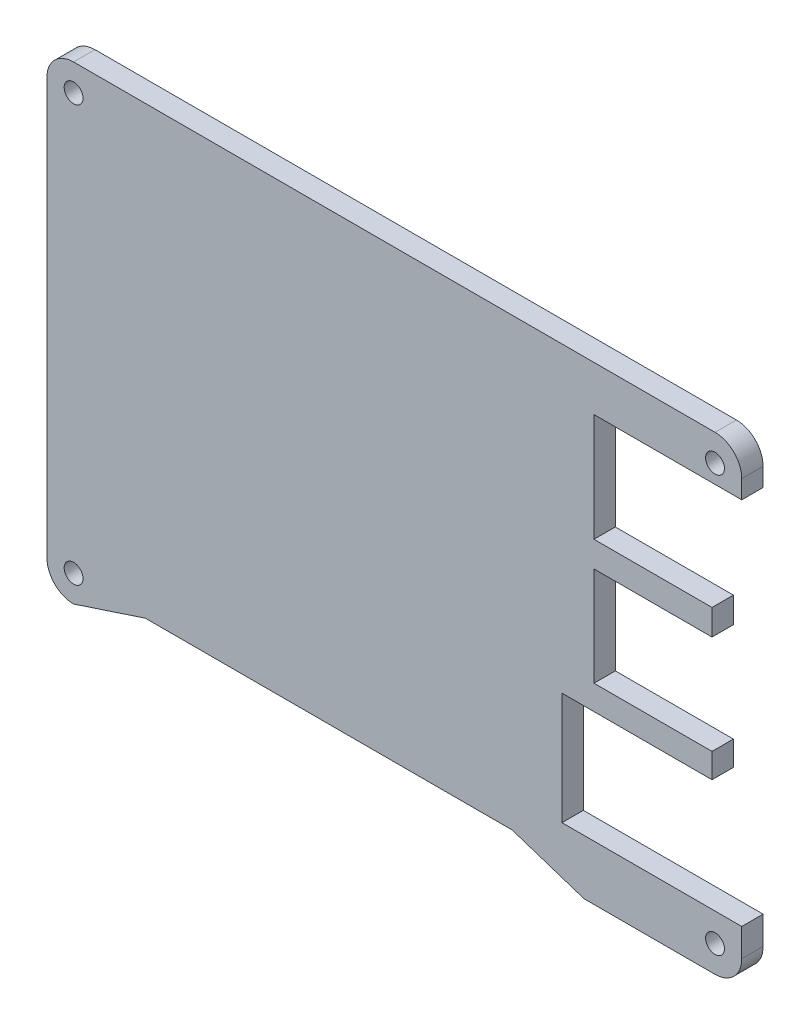
SolidWorks part; units mm, degrees
ref_plane "Front Plane" through (0, 0, 0) normal (0, 0, 1) x (1, 0, 0)
ref_plane "Top Plane" through (0, 0, 0) normal (0, 1, 0) x (1, 0, 0)
ref_plane "Right Plane" through (0, 0, 0) normal (1, 0, 0) x (0, 0, -1)
sketch "Sketch1" plane through (0, 0, 0) normal (0, 0, 1) x (1, 0, 0)
  line L1 (61.2149, 24.0683) -> (61.2149, 26.6839) construction
  line L2 (57.4049, 30.5077) -> (-34.0849, 30.5077) construction
  line L5 (56.975, 4.9979) -> (56.975, 8.6582) construction
  line L9 (56.975, -12.628) -> (56.975, -9.1218) construction
  line L10 (35.575, -12.628) -> (56.975, -12.628) construction
  line L11 (35.575, -28.6278) -> (35.575, -12.628) construction
  line L12 (61.2149, -28.6278) -> (35.575, -28.6278) construction
  line L13 (61.2149, -32.6134) -> (61.2149, -28.6278) construction
  line L14 (38.7143, -36.451) -> (57.405, -36.451) construction
  line L15 (28.4743, -33.0844) -> (38.7143, -36.451) construction
  line L16 (-23.8449, -33.0844) -> (28.4743, -33.0844) construction
  line L17 (-34.0849, -36.451) -> (-23.8449, -33.0844) construction
  line L18 (-37.8949, 26.6977) -> (-37.8949, -32.641) construction
  line L19 (61.2149, 24.0683) -> (40.1348, 24.0683)
  line L20 (61.2149, 24.0683) -> (61.2149, 26.6839)
  line L21 (57.4049, 30.5077) -> (-34.0849, 30.5077)
  line L22 (40.1348, 24.0683) -> (40.1348, 8.6582)
  line L23 (40.1348, 8.6582) -> (56.975, 8.6582)
  line L24 (56.975, 4.9979) -> (56.975, 8.6582)
  line L25 (56.975, 4.9979) -> (40.1348, 4.9979)
  line L26 (40.1348, 4.9979) -> (40.1348, -9.1218)
  line L27 (40.1348, -9.1218) -> (56.975, -9.1218)
  line L28 (56.975, -12.628) -> (56.975, -9.1218)
  line L29 (35.575, -12.628) -> (56.975, -12.628)
  line L30 (35.575, -28.6278) -> (35.575, -12.628)
  line L31 (61.2149, -28.6278) -> (35.575, -28.6278)
  line L32 (61.2149, -32.6134) -> (61.2149, -28.6278)
  line L33 (38.7143, -36.451) -> (57.405, -36.451)
  line L34 (28.4743, -33.0844) -> (38.7143, -36.451)
  line L35 (-23.8449, -33.0844) -> (28.4743, -33.0844)
  line L36 (-34.0849, -36.451) -> (-23.8449, -33.0844)
  line L37 (-37.8949, 26.6977) -> (-37.8949, -32.641)
  line L38 (-23.4169, -23.6989) -> (-23.4169, 9.8012) construction
  line L39 (-29.0049, 25.897) -> (31.6883, 25.897)
  line L40 (-29.0049, 25.897) -> (-29.0049, 18.087)
  line L41 (-29.0049, 18.087) -> (31.6883, 18.087)
  line L42 (31.6883, 25.897) -> (31.6883, 18.087)
  line L43 (-29.0049, 9.8012) -> (-23.4169, 9.8012)
  line L44 (-29.0049, 9.8012) -> (-29.0049, -13.5668)
  line L45 (-29.0049, -13.5668) -> (-23.4169, -13.5668)
  line L46 (-23.4169, 9.8012) -> (-23.4169, -13.5668)
  line L47 (-29.0049, 9.2932) -> (-23.4169, 9.2932)
  line L50 (13.845, -8.3602) -> (19.2484, -8.3602)
  line L51 (13.845, -8.3602) -> (13.845, -30.9668)
  line L52 (13.845, -30.9668) -> (19.2484, -30.9668)
  line L53 (19.2484, -8.3602) -> (19.2484, -30.9668)
  arc A0 (61.2149, 26.6839) -> (57.4049, 30.5077) centre (57.4049, 26.6977) ccw construction
  circle A1 centre (57.4049, 26.6977) radius 1.3462 construction
  arc A2 (57.405, -36.451) -> (61.2149, -32.6134) centre (57.405, -32.641) ccw construction
  arc A3 (-37.8949, -32.641) -> (-34.0849, -36.451) centre (-34.0849, -32.641) ccw construction
  arc A4 (-34.0849, 30.5077) -> (-37.8949, 26.6977) centre (-34.0849, 26.6977) ccw construction
  circle A5 centre (-34.0849, 26.6977) radius 1.3462 construction
  circle A6 centre (-34.0849, -32.641) radius 1.3462 construction
  arc A7 (61.2149, 26.6839) -> (57.4049, 30.5077) centre (57.4049, 26.6977) ccw
  circle A8 centre (57.4049, 26.6977) radius 1.3462
  arc A9 (57.405, -36.451) -> (61.2149, -32.6134) centre (57.405, -32.641) ccw
  arc A10 (-37.8949, -32.641) -> (-34.0849, -36.451) centre (-34.0849, -32.641) ccw
  arc A11 (-34.0849, 30.5077) -> (-37.8949, 26.6977) centre (-34.0849, 26.6977) ccw
  circle A12 centre (-34.0849, 26.6977) radius 1.3462
  circle A13 centre (-34.0849, -32.641) radius 1.3462
  circle A14 centre (57.405, -32.641) radius 1.3462 construction
  circle A15 centre (57.405, -32.641) radius 1.3462
  dimension "D1" = 23.368
  dimension "D2" = 0.508
  dimension "D3" = 16.8402
  dimension "D4" = 16.8402
extrude "Boss-Extrude1" add sketch "Sketch1" along normal blind 3.048
sketch "Sketch2" plane through (0, 0, 3.048) normal (0, 0, 1) x (1, 0, 0)
  line L2 (-37.8949, 26.6977) -> (-37.8949, -32.641) construction
  line L5 (57.4049, 30.5077) -> (-34.0849, 30.5077) construction
  line L6 (-10.2851, -8.9639) -> (-10.2851, 8.0033) construction
  line L7 (-8.7865, -10.4625) -> (8.1807, -10.4625) construction
  line L8 (9.6793, -8.9639) -> (9.6793, 8.0033) construction
  line L9 (8.1807, 9.5019) -> (-8.7865, 9.5019) construction
  line L10 (-10.2851, -10.4625) -> (9.6793, 9.5019) construction
  circle A0 centre (-0.3029, -0.4803) radius 10.922
  circle A1 centre (-10.2851, -10.4625) radius 1.4986
  circle A2 centre (-10.2851, 9.5019) radius 1.4986
  circle A3 centre (9.6793, -10.4625) radius 1.4986
  circle A4 centre (9.6793, 9.5019) radius 1.4986
  dimension "D1" = 26.67
  dimension "D2" = 20.066
  dimension "D3" = 21.844
  dimension "D4" = 16.9672
  dimension "D5" = 2.9972
extrude "Cut-Extrude1" cut sketch "Sketch2" against normal through all
sketch "Sketch3" plane through (0, 0, 3.048) normal (0, 0, 1) x (1, 0, 0)
  line L0 (13.845, -30.9668) -> (19.2484, -30.9668) construction
  line L1 (-29.0049, 25.897) -> (31.6883, 25.897)
  line L2 (-29.0049, 25.897) -> (-29.0049, -30.9668)
  line L3 (-29.0049, -30.9668) -> (31.6883, -30.9668)
  line L4 (31.6883, 25.897) -> (31.6883, -30.9668)
  line L5 (31.6883, 25.897) -> (31.6883, 18.087) construction
extrude "Boss-Extrude2" add sketch "Sketch3" against normal up to vertex (3.048 mm away) up to point (-29.0049, 25.897, 0)
sketch "Sketch4" [suppressed] plane through (0, 0, 3.048) normal (0, 0, 1) x (1, 0, 0)
  circle A0 centre (57.4049, 26.6977) radius 1.524
  circle A1 centre (57.405, -32.641) radius 1.524
  circle A2 centre (-34.0849, -32.641) radius 1.524
  circle A3 centre (-34.0849, 26.6977) radius 1.524
  dimension "D1" = 3.048
extrude "Cut-Extrude2" [suppressed] cut sketch "Sketch4" against normal through all
